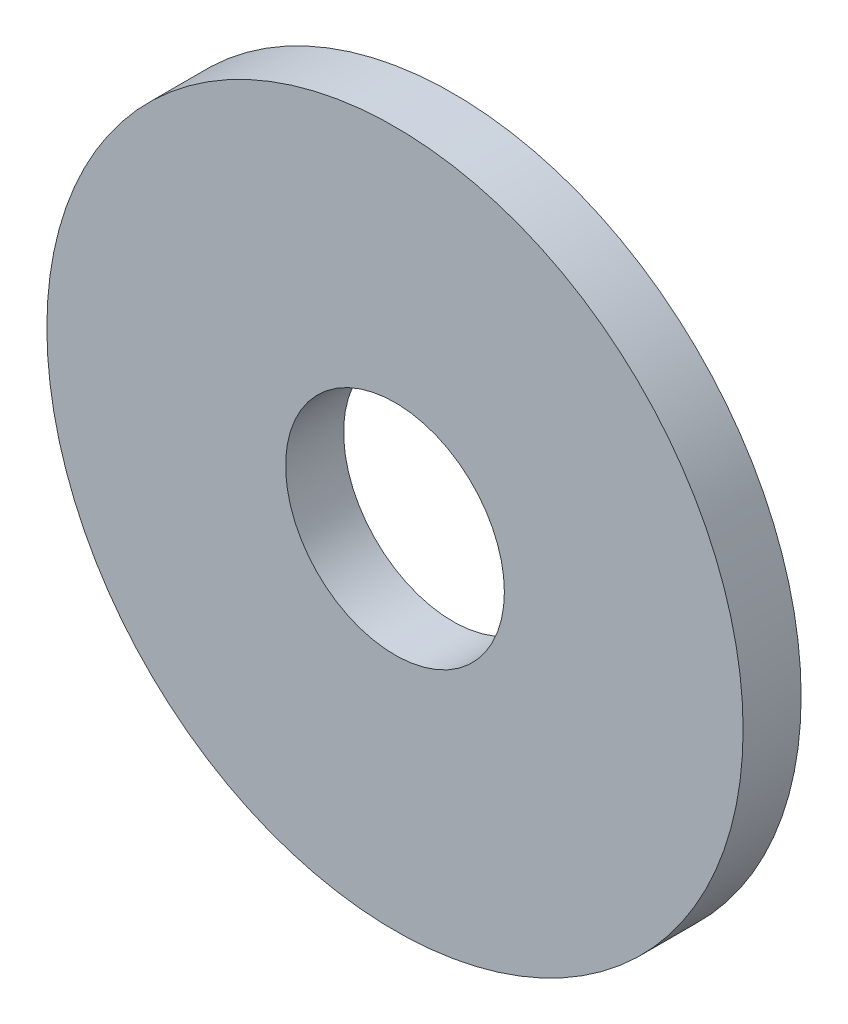
SolidWorks part; units mm, degrees
ref_plane "Front Plane" through (0, 0, 0) normal (0, 0, 1) x (1, 0, 0)
ref_plane "Top Plane" through (0, 0, 0) normal (0, 1, 0) x (1, 0, 0)
ref_plane "Right Plane" through (0, 0, 0) normal (1, 0, 0) x (0, 0, -1)
sketch "Sketch1" plane through (0, 0, 0) normal (0, 0, 1) x (1, 0, 0)
  circle A0 centre (0, 0) radius 2.993
  circle A1 centre (0, 0) radius 9.525
  dimension "D1" = 5.986
  dimension "D2" = 19.05
extrude "Boss-Extrude1" add sketch "Sketch1" along normal blind 1.5875
